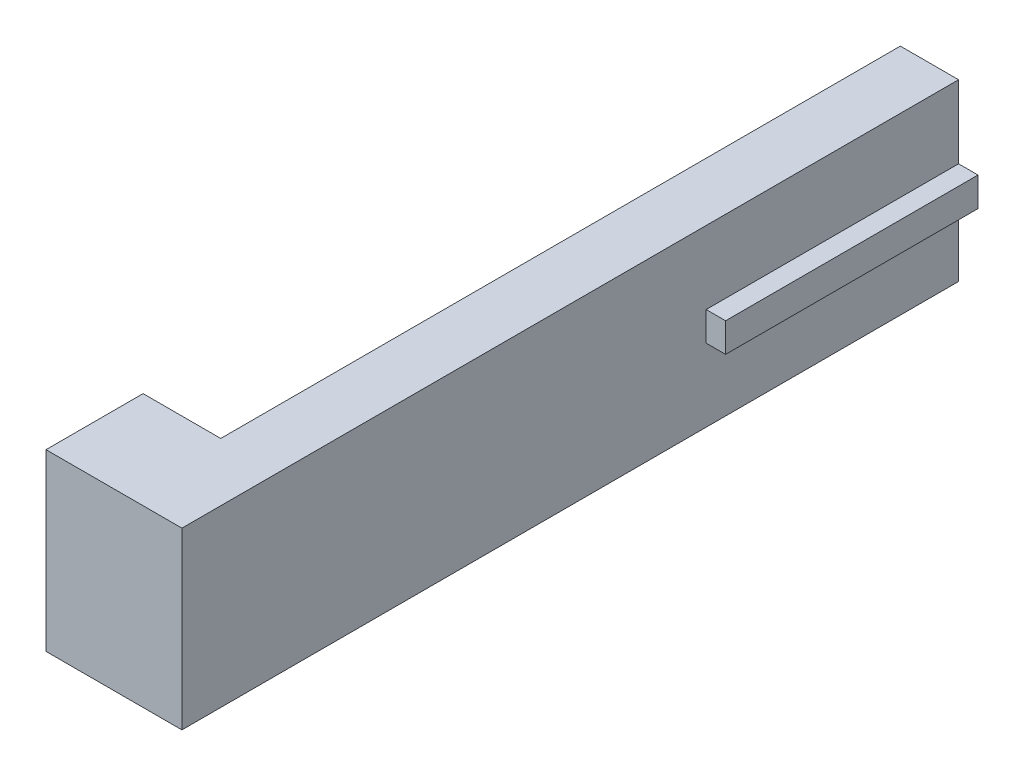
SolidWorks part; units mm, degrees
ref_plane "Front Plane" through (0, 0, 0) normal (0, 0, 1) x (1, 0, 0)
ref_plane "Top Plane" through (0, 0, 0) normal (0, 1, 0) x (1, 0, 0)
ref_plane "Right Plane" through (0, 0, 0) normal (1, 0, 0) x (0, 0, -1)
sketch "Sketch4" plane through (0, 0, 0) normal (0, 0, 1) x (1, 0, 0)
  line L0 (0, -3.75) -> (0, 3.75) construction
  line L1 (5, -3.75) -> (0, -3.75)
  line L2 (5, -3.75) -> (5, 3.75)
  line L3 (5, 3.75) -> (0, 3.75)
  line L4 (0, -3.75) -> (0, 3.75) construction
  line L5 (5, -3.75) -> (0, 3.75) construction
  line L6 (5, 3.75) -> (0, -3.75) construction
  line L7 (-15, -22.5) -> (0, -22.5)
  line L8 (-15, -22.5) -> (-15, 22.5)
  line L9 (-15, 22.5) -> (0, 22.5)
  line L10 (0, -22.5) -> (0, -3.75)
  line L11 (-15, -22.5) -> (0, 22.5) construction
  line L12 (-15, 22.5) -> (0, -22.5) construction
  line L13 (0, 3.75) -> (0, 22.5)
  point P0 (2.5, 0)
  point P5 (0, 0)
  point P7 (-7.5, 0)
  point P12 (0, 0)
  dimension "D1" = 5
  dimension "D2" = 7.5
  dimension "D3" = 45
  dimension "D4" = 15
extrude "Boss-Extrude3" add sketch "Sketch4" along normal blind 200
sketch "Sketch5" plane through (5, 0, 0) normal (1, 0, 0) x (0, 0, -1)
  line L0 (-200, -3.75) -> (0, -3.75) construction
  line L1 (-200, 3.75) -> (0, 3.75) construction
  line L2 (-200, -3.75) -> (-200, 3.75) construction
  line L3 (-200, -3.75) -> (-65, -3.75)
  line L4 (-200, 3.75) -> (-65, 3.75)
  line L5 (-200, -3.75) -> (-200, 3.75)
  line L6 (-65, 3.75) -> (-65, -3.75)
  line L7 (-65, 3.75) -> (0, 3.75) construction
  line L8 (-65, -3.75) -> (0, -3.75) construction
  line L9 (0, -3.75) -> (0, 3.75) construction
  dimension "D1" = 65
extrude "Cut-Extrude1" cut sketch "Sketch5" against normal up to surface (5 mm away) up to face at (0, 13.125, 100)
sketch "Sketch6" plane through (0, 0, 200) normal (0, 0, 1) x (1, 0, 0)
  line L0 (0, -22.5) -> (0, 22.5) construction
  line L1 (-35, -22.5) -> (-15, -22.5)
  line L2 (-35, -22.5) -> (-35, 22.5)
  line L3 (-35, 22.5) -> (-15, 22.5)
  line L4 (-15, -22.5) -> (-15, 22.5)
  line L5 (-35, -22.5) -> (-15, 22.5) construction
  line L6 (-35, 22.5) -> (-15, -22.5) construction
  line L7 (-15, -22.5) -> (0, -22.5) construction
  point P0 (-25, 0)
  dimension "D1" = 35
extrude "Boss-Extrude4" add sketch "Sketch6" against normal blind 25
sketch "Sketch7" plane through (0, 0, 0) normal (0, 0, -1) x (-1, 0, 0)
  line L0 (15, -22.5) -> (15, 22.5) construction
  line L1 (10, -3.75) -> (15, -3.75)
  line L2 (10, -3.75) -> (10, 3.75)
  line L3 (10, 3.75) -> (15, 3.75)
  line L4 (15, -3.75) -> (15, 3.75)
  line L5 (10, -3.75) -> (15, 3.75) construction
  line L6 (10, 3.75) -> (15, -3.75) construction
  line L7 (-5, 3.75) -> (0, 3.75) construction
  point P0 (12.5, 0)
  point P7 (0, 0)
  dimension "D1" = 5
extrude "Cut-Extrude2" cut sketch "Sketch7" against normal up to surface (175 mm away) up to face at (-25, 0, 175)
